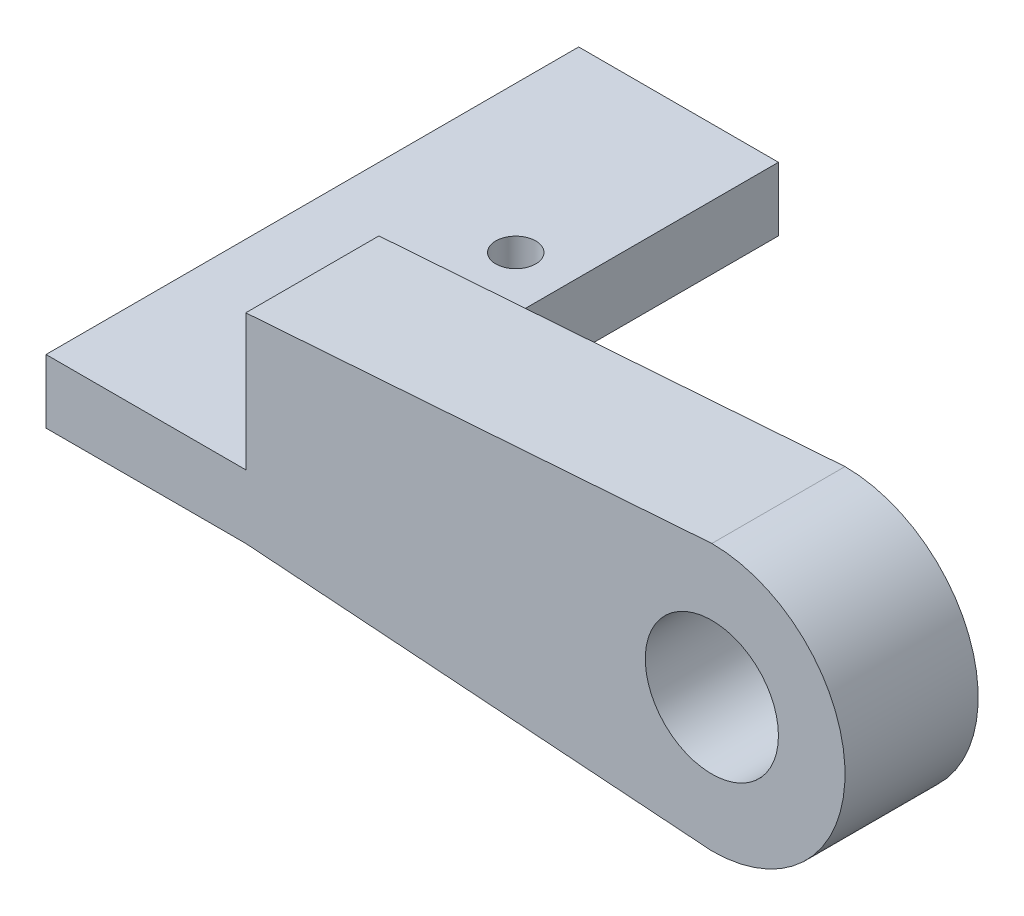
SolidWorks part; units mm, degrees
ref_plane "Front Plane" through (0, 0, 0) normal (0, 0, 1) x (1, 0, 0)
ref_plane "Top Plane" through (0, 0, 0) normal (0, 1, 0) x (1, 0, 0)
ref_plane "Right Plane" through (0, 0, 0) normal (1, 0, 0) x (0, 0, -1)
sketch "Sketch1" plane through (0, 0, 0) normal (0, 0, 1) x (1, 0, 0)
  line L0 (0, 10) -> (-35, 7.5)
  line L1 (-35, 7.5) -> (-35, -7.5)
  line L2 (-35, -7.5) -> (0, -10)
  circle A0 centre (0, 0) radius 5
  arc A1 (0, -10) -> (0, 10) centre (0, 0) ccw
  circle A2 centre (0, 0) radius 10 construction
  point P4 (-35, 0)
  dimension "D1" = 10
  dimension "D3" = 35
  dimension "D4" = 15
  dimension "D2" = 5
extrude "Boss-Extrude1" add sketch "Sketch1" along normal blind 10
sketch "Sketch2" plane through (0, 0, 0) normal (0, 0, -1) x (-1, 0, 0)
  line L0 (35, 7.5) -> (35, -7.5) construction
  line L1 (35, -2.711) -> (20, -2.711)
  line L2 (35, -2.711) -> (35, -7.711)
  line L3 (35, -7.711) -> (20, -7.711)
  line L4 (20, -2.711) -> (20, -7.711)
  dimension "D1" = 15
  dimension "D2" = 5
sketch "Sketch3" plane through (-35, 0, 0) normal (-1, 0, 0) x (0, 0, 1)
  line L0 (10, -7.5) -> (10, -10) construction
  line L1 (0, -2.711) -> (10, -2.711)
  line L2 (0, -2.711) -> (0, -7.5)
  line L3 (0, -7.5) -> (10, -7.5)
  line L4 (10, -2.711) -> (10, -7.5)
  line L5 (10, -7.5) -> (0, -7.5) construction
  line L6 (0, 7.5) -> (0, -7.5) construction
  dimension "D1" = 4.789
extrude "Boss-Extrude2" add sketch "Sketch3" along normal blind 15
sketch "Sketch4" plane through (0, 0, 0) normal (0, 0, -1) x (-1, 0, 0)
  line L0 (50, -2.711) -> (35, -2.711) construction
  line L1 (35, -2.711) -> (50, -2.711)
  line L2 (35, -2.711) -> (35, -7.5)
  line L3 (35, -7.5) -> (50, -7.5)
  line L4 (50, -2.711) -> (50, -7.5)
  line L5 (50, -7.5) -> (35, -7.5) construction
  dimension "D1" = 15
extrude "Boss-Extrude3" add sketch "Sketch4" along normal blind 30
sketch "Sketch5" plane through (0, -2.711, 0) normal (0, 1, 0) x (1, 0, 0)
  circle A2 centre (-39, 2.2735) radius 1.5
  circle A3 centre (-39, 14.2735) radius 1.5
extrude "Cut-Extrude1" cut sketch "Sketch5" against normal up to next
sketch "Sketch6" plane through (0, -7.5, 0) normal (0, -1, 0) x (1, 0, 0)
  line L0 (-50, -7.4186) -> (-50, -24.1283)
  line L5 (-35, 0) -> (-35, 10)
  line L6 (-35, 10) -> (-50, 10)
  line L7 (-50, 10) -> (-50, -30)
  line L8 (-50, -30) -> (-35, -30)
  line L9 (-35, -30) -> (-35, 0)
  line L12 (-50, -7.4186) -> (-50, -24.1283)
  arc A1 (-50, -24.1283) -> (-50, -7.4186) centre (-52.5997, -15.7735) ccw
  point P6 (0, 0)
  point P9 (0, 0)
  point P10 (0, 0)
  point P11 (0, 0)
  point P12 (0, 0)
  dimension "D1" = 0
